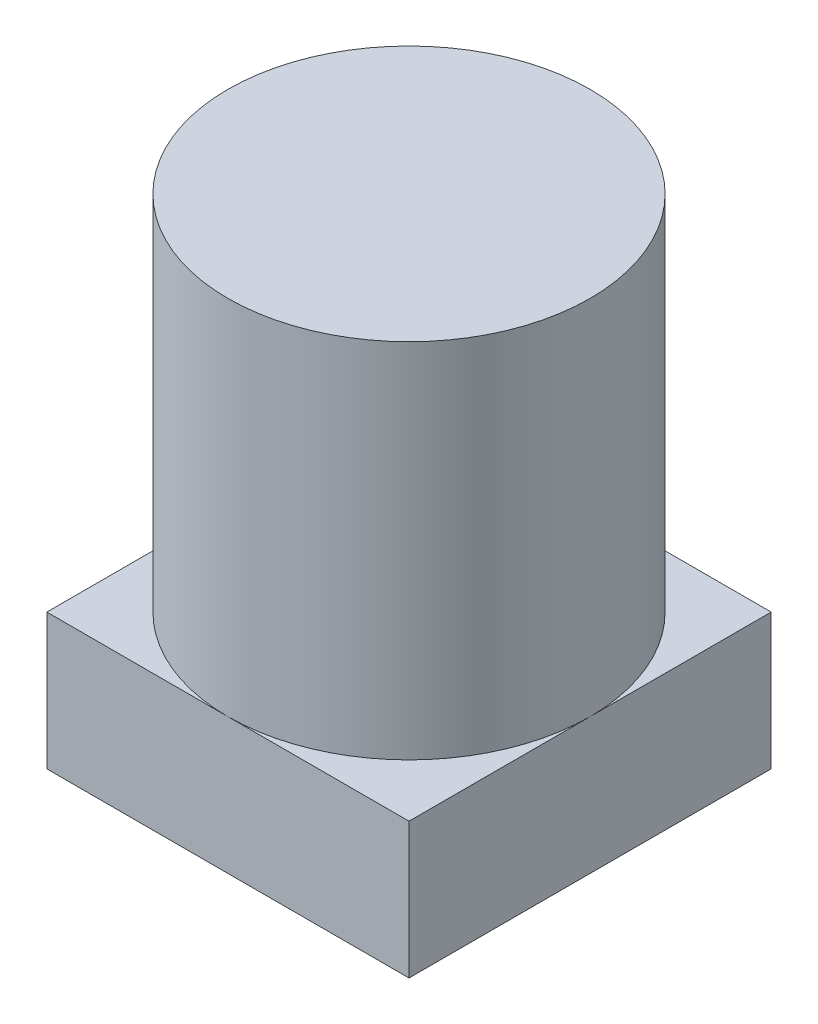
SolidWorks part; units mm, degrees
ref_plane "Front Plane" through (0, 0, 0) normal (0, 0, 1) x (1, 0, 0)
ref_plane "Top Plane" through (0, 0, 0) normal (0, 1, 0) x (1, 0, 0)
ref_plane "Right Plane" through (0, 0, 0) normal (1, 0, 0) x (0, 0, -1)
sketch "Sketch1" plane through (0, 0, 0) normal (0, 1, 0) x (1, 0, 0)
  line L1 (-2.6903, 2.531) -> (5.3097, 2.531)
  line L2 (-2.6903, 2.531) -> (-2.6903, -5.469)
  line L3 (-2.6903, -5.469) -> (5.3097, -5.469)
  line L4 (5.3097, 2.531) -> (5.3097, -5.469)
  dimension "D1" = 8
  dimension "D2" = 8
extrude "Boss-Extrude1" add sketch "Sketch1" along normal blind 3
sketch "Sketch2" plane through (0, 3, 0) normal (0, 1, 0) x (1, 0, 0)
  line L0 (-2.6903, 2.531) -> (-2.6903, -5.469) construction
  line L1 (5.3097, -5.469) -> (5.3097, 2.531) construction
  line L2 (5.3097, 2.531) -> (-2.6903, 2.531) construction
  circle A0 centre (1.3097, -1.469) radius 4
extrude "Boss-Extrude2" add sketch "Sketch2" along normal blind 8
